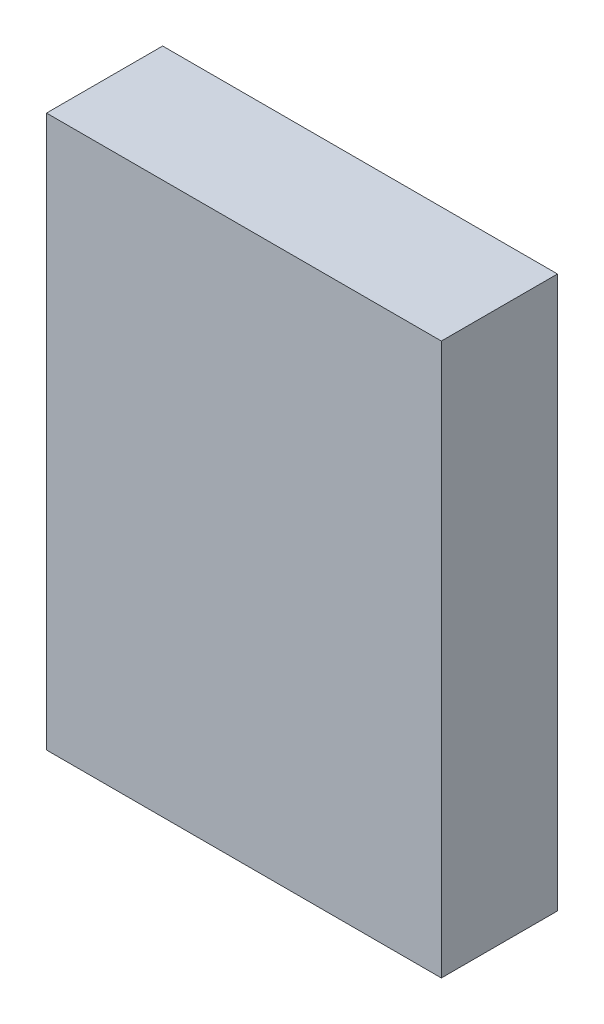
SolidWorks part; units mm, degrees
ref_plane "Front Plane" through (0, 0, 0) normal (0, 0, 1) x (1, 0, 0)
ref_plane "Top Plane" through (0, 0, 0) normal (0, 1, 0) x (1, 0, 0)
ref_plane "Right Plane" through (0, 0, 0) normal (1, 0, 0) x (0, 0, -1)
sketch "Sketch1" plane through (0, 0, 0) normal (0, 1, 0) x (1, 0, 0)
  line L1 (-34, 10) -> (34, 10)
  line L2 (-34, 10) -> (-34, -10)
  line L3 (-34, -10) -> (34, -10)
  line L4 (34, 10) -> (34, -10)
  dimension "D1" = 34
  dimension "D2" = 34
  dimension "D3" = 10
  dimension "D4" = 10
extrude "Boss-Extrude1" add sketch "Sketch1" along normal mid plane 95
